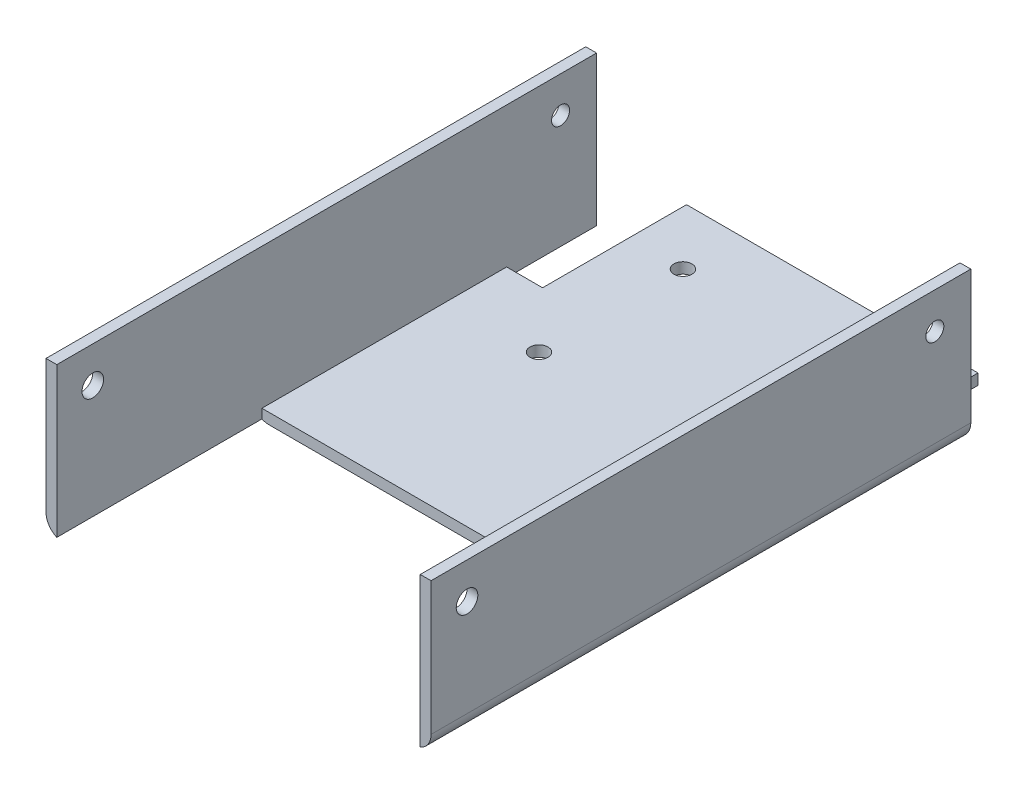
SolidWorks part; units mm, degrees
ref_plane "Alzado" through (0, 0, 0) normal (0, 0, 1) x (1, 0, 0)
ref_plane "Planta" through (0, 0, 0) normal (0, 1, 0) x (1, 0, 0)
ref_plane "Vista lateral" through (0, 0, 0) normal (1, 0, 0) x (0, 0, -1)
sketch "Croquis2" plane through (0, 0, 0) normal (0, 0, 1) x (1, 0, 0)
  line L0 (-85.0135, 0) -> (103.558, 0) construction
  line L1 (61.7398, 10) -> (61.7398, -32)
  line L2 (61.7398, -32) -> (-45.2602, -32)
  line L3 (-45.2602, -32) -> (-45.2602, 10)
  line L4 (61.7398, 10) -> (58.7398, 10)
  line L5 (-45.2602, 10) -> (-42.2602, 10)
  line L6 (-42.2602, -29) -> (58.7398, -29)
  line L7 (58.7398, 10) -> (58.7398, -29)
  line L8 (-42.2602, 10) -> (-42.2602, -29)
  dimension "D1" = 42
  dimension "D2" = 10
  dimension "D3" = 107
  dimension "D4" = 42
  dimension "D5" = 3
  dimension "D6" = 3
  dimension "D7" = 3
extrude "Saliente-Extruir1" add sketch "Croquis2" along normal blind 165
sketch "Croquis3" plane through (0, -29, 0) normal (0, 1, 0) x (1, 0, 0)
  line L1 (-42.2602, 0) -> (-32.2602, 0)
  line L2 (-42.2602, 0) -> (-42.2602, -40)
  line L3 (-42.2602, -40) -> (-32.2602, -40)
  line L4 (-32.2602, 0) -> (-32.2602, -40)
  line L5 (58.7398, 0) -> (48.7398, 0)
  line L6 (58.7398, 0) -> (58.7398, -40)
  line L7 (58.7398, -40) -> (48.7398, -40)
  line L8 (48.7398, 0) -> (48.7398, -40)
  dimension "D1" = 10
  dimension "D2" = 10
  dimension "D3" = 40
  dimension "D4" = 40
extrude "Cortar-Extruir1" cut sketch "Croquis3" against normal blind 165
sketch "Croquis4" plane through (0, 10, 0) normal (0, 1, 0) x (1, 0, 0)
  line L0 (-42.2602, -165) -> (-42.2602, 0) construction
  line L1 (-45.2602, 0) -> (-42.2602, 0)
  line L2 (-45.2602, 0) -> (-45.2602, -15)
  line L3 (-45.2602, -15) -> (-42.2602, -15)
  line L4 (-42.2602, 0) -> (-42.2602, -15)
  line L5 (61.7398, -165) -> (61.7398, 0) construction
  line L6 (58.7398, 0) -> (61.7398, 0)
  line L7 (58.7398, 0) -> (58.7398, -15)
  line L8 (58.7398, -15) -> (61.7398, -15)
  line L9 (61.7398, 0) -> (61.7398, -15)
  dimension "D1" = 15
  dimension "D2" = 15
extrude "Cortar-Extruir2" cut sketch "Croquis4" against normal blind 165
sketch "Croquis5" plane through (0, -29, 0) normal (0, 1, 0) x (1, 0, 0)
  line L0 (58.7398, -165) -> (58.7398, -40) construction
  line L1 (-42.2602, -165) -> (58.7398, -165)
  line L2 (-42.2602, -165) -> (-42.2602, -108)
  line L3 (-42.2602, -108) -> (58.7398, -108)
  line L4 (58.7398, -165) -> (58.7398, -108)
  dimension "D1" = 57
extrude "Cortar-Extruir3" cut sketch "Croquis5" against normal blind 165
sketch "Croquis6" plane through (61.7398, 0, 0) normal (1, 0, 0) x (0, 0, -1)
  line L0 (-15, -32) -> (-15, 10) construction
  line L1 (-165, 10) -> (-15, 10) construction
  line L2 (-165, -32) -> (-165, 10) construction
  circle A0 centre (-25, 0) radius 2.5
  circle A1 centre (-155, 0) radius 2.5
  dimension "D5" = 5
  dimension "D6" = 5
  dimension "D1" = 10
  dimension "D2" = 10
  dimension "D3" = 10
  dimension "D4" = 10
extrude "Cortar-Extruir4" cut sketch "Croquis6" against normal blind 165
fillet "Redondeo1" radius 5 2 edges at (61.7398, -32, 90) (-45.2602, -32, 90)
sketch "Croquis7" plane through (61.7398, 0, 0) normal (1, 0, 0) x (0, 0, -1)
  circle A0 centre (-155, 0) radius 3
extrude "Cortar-Extruir5" cut sketch "Croquis7" against normal blind 110
sketch "Croquis8" plane through (0, -29, 0) normal (0, 1, 0) x (1, 0, 0)
  line L0 (-20.3591, -25) -> (39.2339, -25) construction
  circle A0 centre (-17.2602, -16) radius 2.5
  circle A1 centre (-17.2602, -56) radius 2.5
  dimension "D1" = 5
  dimension "D2" = 5
  dimension "D3" = 40
  dimension "D4" = 10
  dimension "D5" = 9
  dimension "D6" = 25
extrude "Cortar-Extruir6" cut sketch "Croquis8" against normal blind 10
